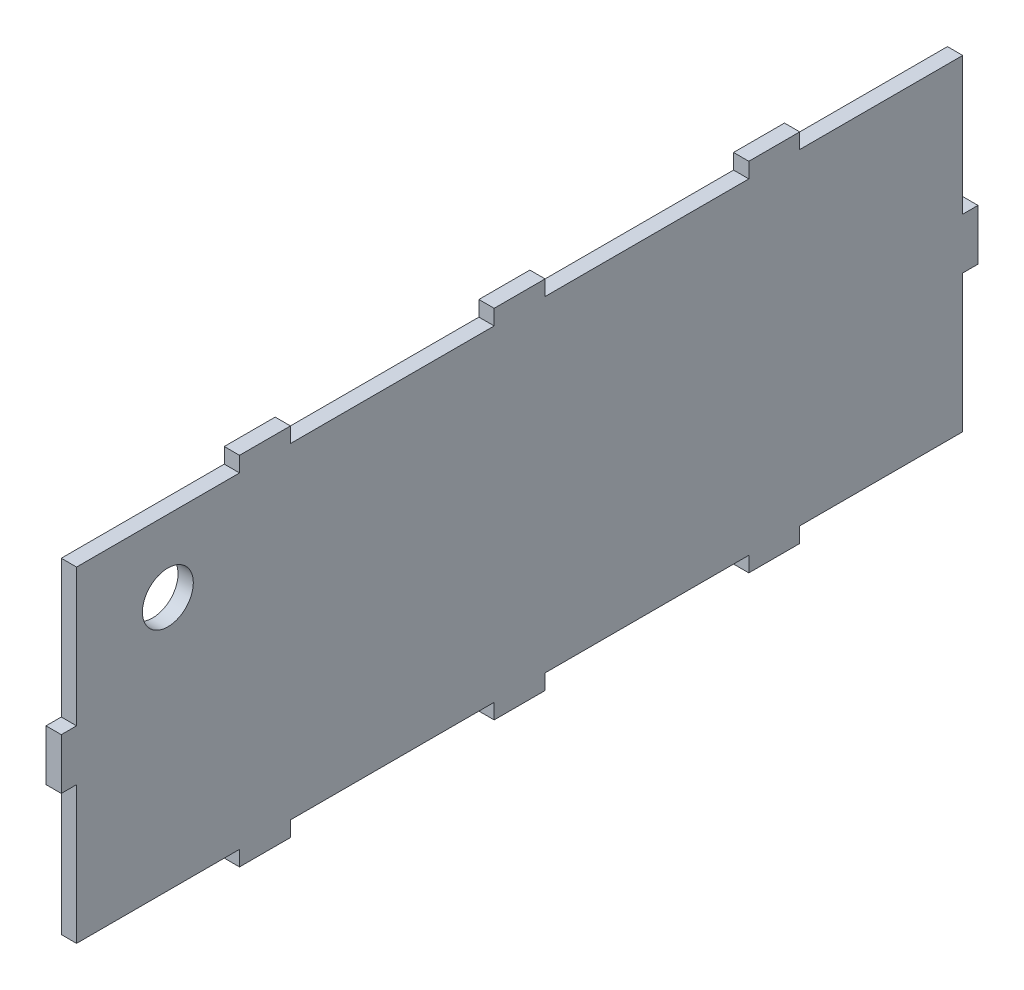
SolidWorks part; units mm, degrees
ref_plane "Front Plane" through (0, 0, 0) normal (0, 0, 1) x (1, 0, 0)
ref_plane "Top Plane" through (0, 0, 0) normal (0, 1, 0) x (1, 0, 0)
ref_plane "Right Plane" through (0, 0, 0) normal (1, 0, 0) x (0, 0, -1)
sketch "Sketch1" plane through (0, 0, 0) normal (1, 0, 0) x (0, 0, -1)
  line L1 (-90, 35) -> (90, 35)
  line L2 (-90, 35) -> (-90, -35)
  line L3 (-90, -35) -> (90, -35)
  line L4 (90, 35) -> (90, -35)
  line L5 (-90, 35) -> (90, -35) construction
  line L6 (-90, -35) -> (90, 35) construction
  point P0 (0, 0)
  dimension "D1" = 180
  dimension "D2" = 70
extrude "Boss-Extrude1" add sketch "Sketch1" along normal blind 3
sketch "Sketch2" plane through (3, 0, 0) normal (1, 0, 0) x (0, 0, -1)
  line L0 (0, 0) -> (0, 35)
  line L1 (90, 35) -> (-90, 35) construction
  line L3 (-90, -35) -> (90, -35) construction
  line L4 (0, 0) -> (90, 0)
  line L5 (90, -35) -> (90, 35) construction
  line L7 (-90, 35) -> (-90, -35) construction
  line L8 (-5, 35) -> (-45, 35)
  line L9 (0, 35) -> (5, 35)
  line L10 (0, 35) -> (0, 32)
  line L11 (0, 32) -> (5, 32)
  line L12 (5, 35) -> (5, 32)
  line L13 (0, 35) -> (-5, 35)
  line L14 (0, 35) -> (0, 32)
  line L15 (0, 32) -> (-5, 32)
  line L16 (-5, 35) -> (-5, 32)
  line L17 (0, -35) -> (5, -35)
  line L18 (0, -35) -> (0, -32)
  line L19 (0, -32) -> (5, -32)
  line L20 (5, -35) -> (5, -32)
  line L21 (0, -35) -> (-5, -35)
  line L22 (0, -35) -> (0, -32)
  line L23 (0, -32) -> (-5, -32)
  line L24 (-5, -35) -> (-5, -32)
  line L25 (90, 0) -> (87, 0)
  line L26 (90, 0) -> (90, 5)
  line L27 (90, 5) -> (87, 5)
  line L28 (87, 0) -> (87, 5)
  line L29 (87, 0) -> (90, 0)
  line L30 (87, 0) -> (87, -5)
  line L31 (87, -5) -> (90, -5)
  line L32 (90, 0) -> (90, -5)
  line L33 (-90, 0) -> (-87, 0)
  line L34 (-90, 0) -> (-90, 5)
  line L35 (-90, 5) -> (-87, 5)
  line L36 (-87, 0) -> (-87, 5)
  line L37 (-90, 0) -> (-87, 0)
  line L38 (-90, 0) -> (-90, -5)
  line L39 (-90, -5) -> (-87, -5)
  line L40 (-87, 0) -> (-87, -5)
  line L41 (-90, 5) -> (-87, 5)
  line L42 (-90, 5) -> (-90, 32)
  line L43 (-90, 32) -> (-87, 32)
  line L44 (-87, 5) -> (-87, 32)
  line L45 (-90, -5) -> (-87, -5)
  line L46 (-90, -5) -> (-90, -32)
  line L47 (-90, -32) -> (-87, -32)
  line L48 (-87, -5) -> (-87, -32)
  line L49 (90, 32) -> (87, 32)
  line L50 (90, 32) -> (90, 5)
  line L51 (90, 5) -> (87, 5)
  line L52 (87, 32) -> (87, 5)
  line L53 (90, -5) -> (87, -5)
  line L54 (90, -5) -> (90, -32)
  line L55 (90, -32) -> (87, -32)
  line L56 (87, -5) -> (87, -32)
  line L74 (-45, 35) -> (-55, 35)
  line L75 (-45, 35) -> (-45, 32)
  line L76 (-45, 32) -> (-55, 32)
  line L77 (-55, 35) -> (-55, 32)
  line L80 (45, 35) -> (45, 32)
  line L81 (45, 32) -> (55, 32)
  line L82 (55, 35) -> (55, 32)
  line L83 (-55, -35) -> (-45, -35)
  line L84 (-55, -35) -> (-55, -32)
  line L85 (-55, -32) -> (-45, -32)
  line L86 (-45, -35) -> (-45, -32)
  line L87 (45, -35) -> (55, -35)
  line L88 (45, -35) -> (45, -32)
  line L89 (45, -32) -> (55, -32)
  line L90 (55, -35) -> (55, -32)
  line L91 (-55, -35) -> (-90, -35)
  line L92 (-55, -35) -> (-55, -32)
  line L93 (-55, -32) -> (-90, -32)
  line L94 (-90, -35) -> (-90, -32)
  line L95 (-5, -35) -> (-45, -35)
  line L96 (-5, -35) -> (-5, -32)
  line L97 (-5, -32) -> (-45, -32)
  line L98 (-45, -35) -> (-45, -32)
  line L99 (45, -35) -> (5, -35)
  line L100 (45, -35) -> (45, -32)
  line L101 (45, -32) -> (5, -32)
  line L102 (5, -35) -> (5, -32)
  line L103 (90, -35) -> (55, -35)
  line L104 (90, -35) -> (90, -32)
  line L105 (90, -32) -> (55, -32)
  line L106 (55, -35) -> (55, -32)
  line L107 (90, 32) -> (55, 32)
  line L108 (90, 32) -> (90, 35)
  line L110 (55, 32) -> (55, 35)
  line L111 (45, 32) -> (5, 32)
  line L112 (45, 32) -> (45, 35)
  line L114 (5, 32) -> (5, 35)
  line L115 (-5, 32) -> (-45, 32)
  line L116 (-5, 32) -> (-5, 35)
  line L117 (-5, 35) -> (-45, 35)
  line L118 (-45, 32) -> (-45, 35)
  line L119 (-55, 32) -> (-90, 32)
  line L120 (-55, 32) -> (-55, 35)
  line L121 (-55, 35) -> (-90, 35)
  line L122 (-90, 32) -> (-90, 35)
  line M16 (90, -35) -> (90, 35)
  line M17 (90, 35) -> (-90, 35)
  line M18 (-90, 35) -> (-90, -35)
  line M19 (-90, -35) -> (90, -35)
  dimension "D1" = 3
  dimension "D2" = 5
  dimension "D3" = 5
  dimension "D4" = 5
  dimension "D5" = 3
  dimension "D6" = 5
  dimension "D7" = 5
  dimension "D8" = 3
  dimension "D9" = 3
  dimension "D10" = 5
  dimension "D11" = 40
  dimension "D12" = 10
  dimension "D13" = 3
  dimension "D15" = 10
extrude "Cut-Extrude6" cut sketch "Sketch2" against normal blind 10 contours L55 L105 L90 M19 M16 | L31 L56 L55 M16 | L88 L101 L20 M19 | L24 L97 L86 M19 | L84 L93 L47 M18 M19 | L48 L39 L47 M18 | L35 L44 L43 M18 | L119 L77 L43 M17 M18 | L115 L16 L75 M17 | L111 L80 L12 M17 | L107 L49 L82 M16 M17 | L49 L52 L27 M16
sketch "Sketch3" plane through (3, 0, 0) normal (1, 0, 0) x (0, 0, -1)
  circle A0 centre (-69.0724, 17.8732) radius 5
extrude "Cut-Extrude7" cut sketch "Sketch3" against normal blind 12 contours A0
